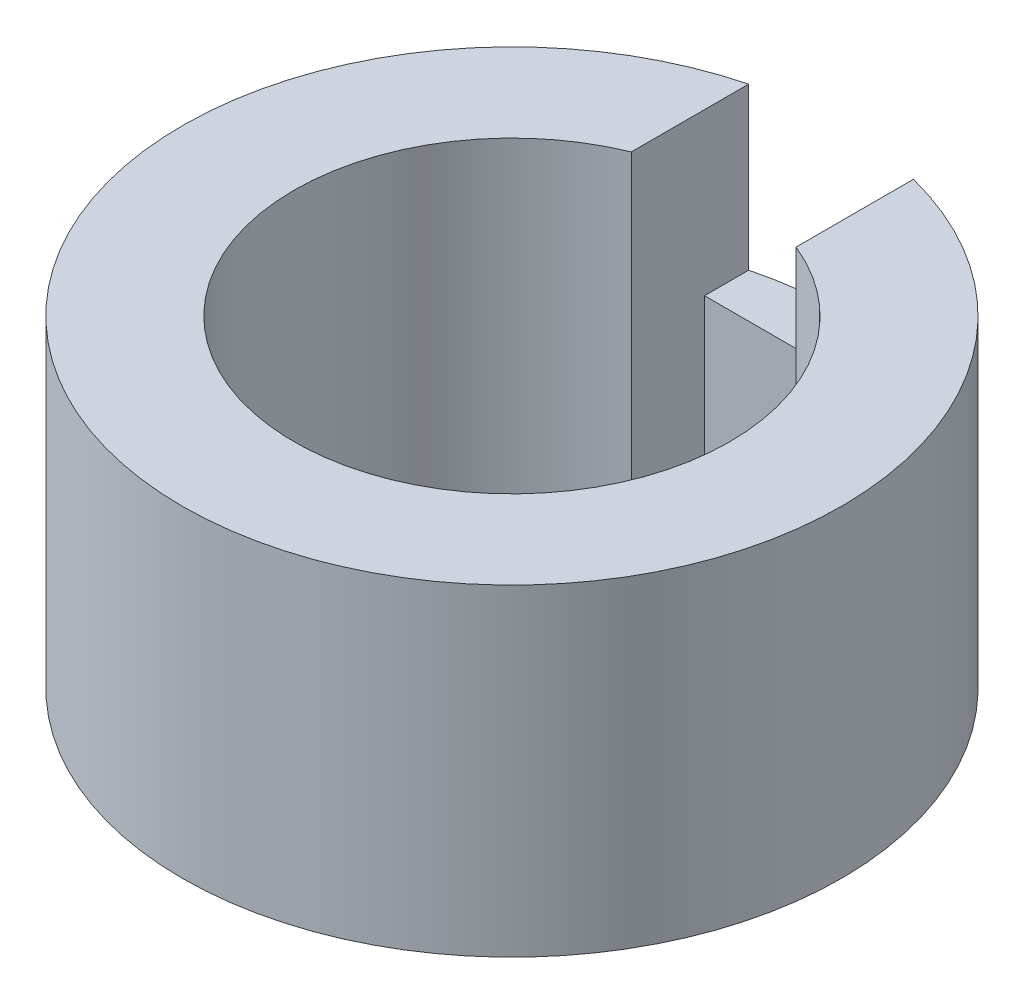
SolidWorks part; units mm, degrees
ref_plane "Front Plane" through (0, 0, 0) normal (0, 0, 1) x (1, 0, 0)
ref_plane "Top Plane" through (0, 0, 0) normal (0, 1, 0) x (1, 0, 0)
ref_plane "Right Plane" through (0, 0, 0) normal (1, 0, 0) x (0, 0, -1)
sketch "Sketch1" plane through (0, 0, 0) normal (0, 1, 0) x (1, 0, 0)
  line L0 (-2.25, 5.5082) -> (-2.25, 7.5082)
  line L1 (-2.25, 7.5082) -> (2.25, 7.5082)
  line L2 (2.25, 7.5082) -> (2.25, 5.5082)
  circle A0 centre (0, 0) radius 5.95
  circle A1 centre (0, 0) radius 9
  point P6 (0, 7.5082)
  dimension "D1" = 11.9
  dimension "D2" = 18
  dimension "D3" = 4.5
  dimension "D4" = 2
extrude "Boss-Extrude1" add sketch "Sketch1" along normal blind 8.8 contours A1 A0 L0 L1 L2
sketch "Sketch2" plane through (0, 0, 0) normal (0, 0, 1) x (1, 0, 0)
  line L0 (5.95, 8.8) -> (-5.95, 8.8) construction
  line L1 (-2.25, 8.8) -> (2.25, 8.8)
  line L2 (-2.25, 8.8) -> (-2.25, 4.4)
  line L3 (-2.25, 4.4) -> (2.25, 4.4)
  line L4 (2.25, 8.8) -> (2.25, 4.4)
  point P6 (0, 4.4)
  dimension "D1" = 4.5
  dimension "D2" = 4.4
extrude "Cut-Extrude1" cut sketch "Sketch2" against normal through all
